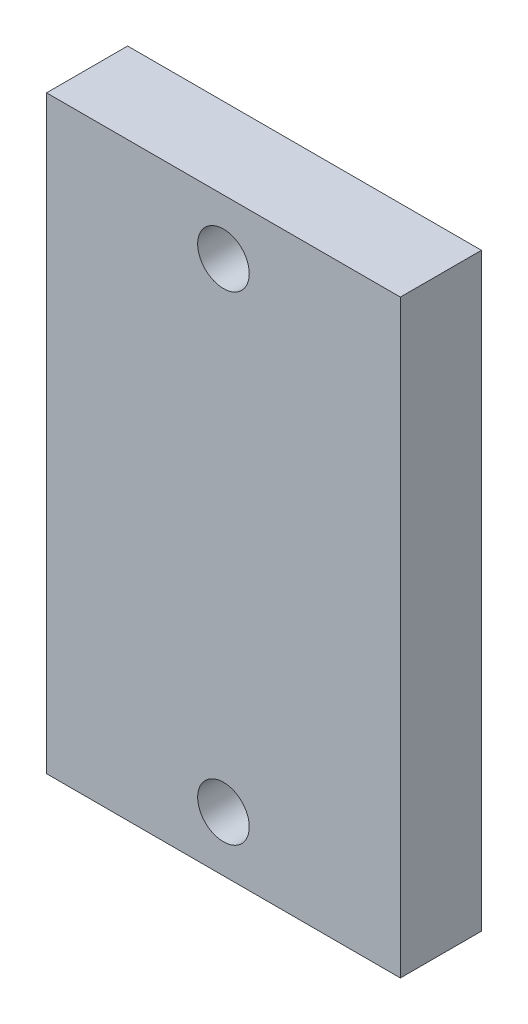
SolidWorks part; units mm, degrees
ref_plane "Alzado" through (0, 0, 0) normal (0, 0, 1) x (1, 0, 0)
ref_plane "Planta" through (0, 0, 0) normal (0, 1, 0) x (1, 0, 0)
ref_plane "Vista lateral" through (0, 0, 0) normal (1, 0, 0) x (0, 0, -1)
sketch "Croquis1" plane through (0, 0, 0) normal (0, 0, 1) x (1, 0, 0)
  line L1 (12, -20) -> (-12, -20)
  line L2 (12, -20) -> (12, 20)
  line L3 (12, 20) -> (-12, 20)
  line L4 (-12, -20) -> (-12, 20)
  line L5 (12, -20) -> (-12, 20) construction
  line L6 (12, 20) -> (-12, -20) construction
  circle A0 centre (0, 16.25) radius 1.75
  circle A1 centre (0, -16.25) radius 1.75
  point P0 (0, 0)
  point P10 (0, -20)
  dimension "D3" = 3.5
  dimension "D4" = 3.5
  dimension "D1" = 40
  dimension "D2" = 24
  dimension "D5" = 32.5
  dimension "D6" = 3.75
extrude "Saliente-Extruir1" add sketch "Croquis1" along normal blind 5.5
